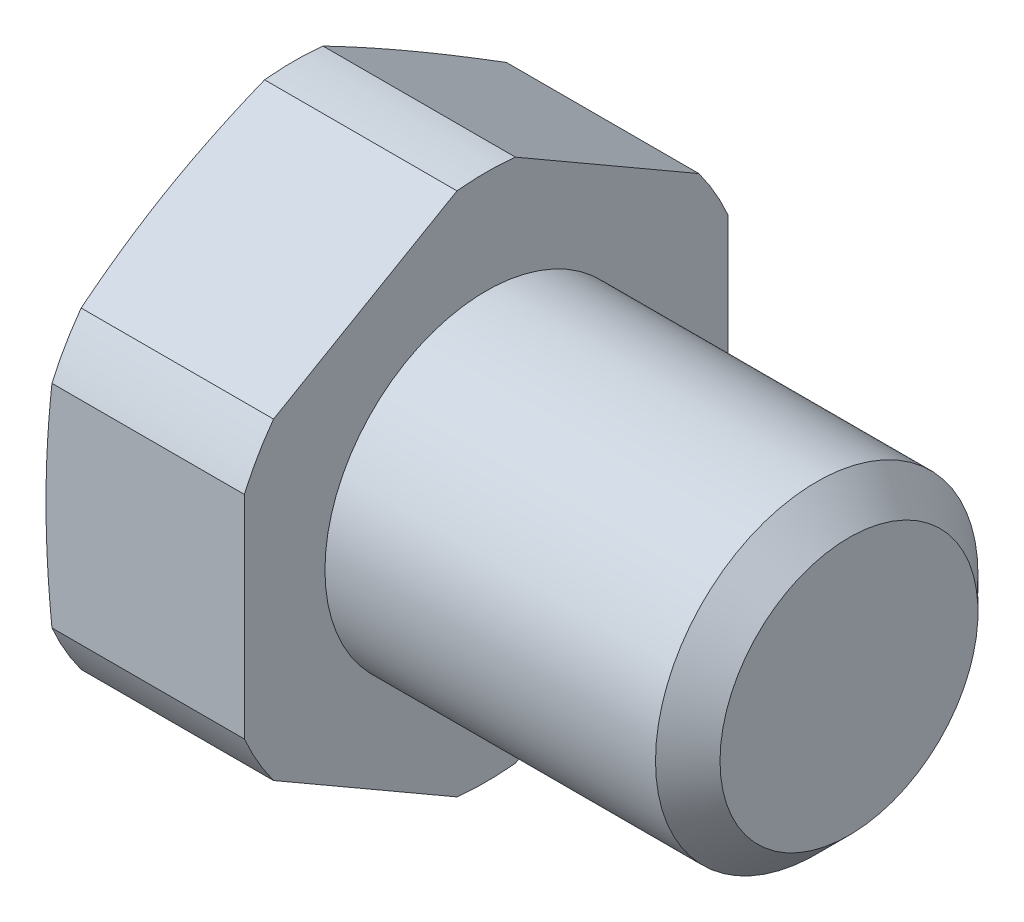
SolidWorks part; units mm, degrees
material "AISI 1020"
ref_plane "Спереди" through (0, 0, 0) normal (0, 0, 1) x (1, 0, 0)
ref_plane "Сверху" through (0, 0, 0) normal (0, 1, 0) x (1, 0, 0)
ref_plane "Справа" through (0, 0, 0) normal (1, 0, 0) x (0, 0, -1)
sketch "Эскиз1" plane through (0, 0, 0) normal (0, 0, 1) x (1, 0, 0)
  line L0 (-1000, 0) -> (49000, 0) construction
  line L1 (-10, 0) -> (-10, 11.4)
  line L2 (-10, 11.4) -> (-9.5445, 13.1)
  line L3 (-9.5445, 13.1) -> (0, 13.1)
  line L4 (0, 13.1) -> (0, 8)
  line L5 (0, 8) -> (16.4, 8)
  line L6 (18, 6.4) -> (18, 0)
  line L7 (18, 8) -> (19, 9.7321) construction
  line L8 (19, 9.7321) -> (20, 8) construction
  line L9 (20, 8) -> (18, 8) construction
  line L10 (19, 9.7321) -> (19, 8) construction
  line L11 (19, 9.7321) -> (1, 9.7321) construction
  line L12 (16.4, 8) -> (18, 6.4)
  line L13 (18, 8) -> (17.2, 7.2) construction
  line L14 (-10, 11.4) -> (-34, 11.4) construction
  line L15 (-10, 0) -> (18, 0)
  dimension "l_" = 18
  dimension "b_" = 18
  dimension "_d_" = 16
  dimension "D" = 22.8
  dimension "k_" = 10
  dimension "e_" = 26.2
  dimension "shag_" = 2
  dimension "dr" = 1.7321
  dimension "D1" = 1.6
  dimension "D2" = 15
  dimension "S_" = 24
revolve "Повернуть1" add sketch "Эскиз1" angle 360 about L0
cosmetic thread "Условное изображение резьбы1" parameters "D1"=18, "D2"=12.5359
sketch "Эскиз2" plane through (-10, 0, 0) normal (-1, 0, 0) x (0, 0, 1)
  line L1 (0, 13.8564) -> (-12, 6.9282)
  line L2 (-12, 6.9282) -> (-12, -6.9282)
  line L3 (-12, -6.9282) -> (0, -13.8564)
  line L4 (0, -13.8564) -> (12, -6.9282)
  line L5 (12, -6.9282) -> (12, 6.9282)
  line L6 (12, 6.9282) -> (0, 13.8564)
  circle A0 centre (0, 0) radius 12 construction
  dimension "D1" = 24
extrude "Вырез-Вытянуть1" cut sketch "Эскиз2" against normal up to surface (28 mm away) flip side to cut up to face at (18, 0, 6.4)
equation "\"D1@Эскиз1\"=\"_d_@Эскиз1\"/10"
equation "\"D@Эскиз1\"=\"S_@Эскиз1\"*0.95"
equation "\"D1@Эскиз2\"=\"S_@Эскиз1\""
equation "\"D1@Условное изображение резьбы1\"=\"b_@Эскиз1\""
equation "\"D2@Условное изображение резьбы1\"=\"_d_@Эскиз1\"-\"dr@Эскиз1\"*2"
